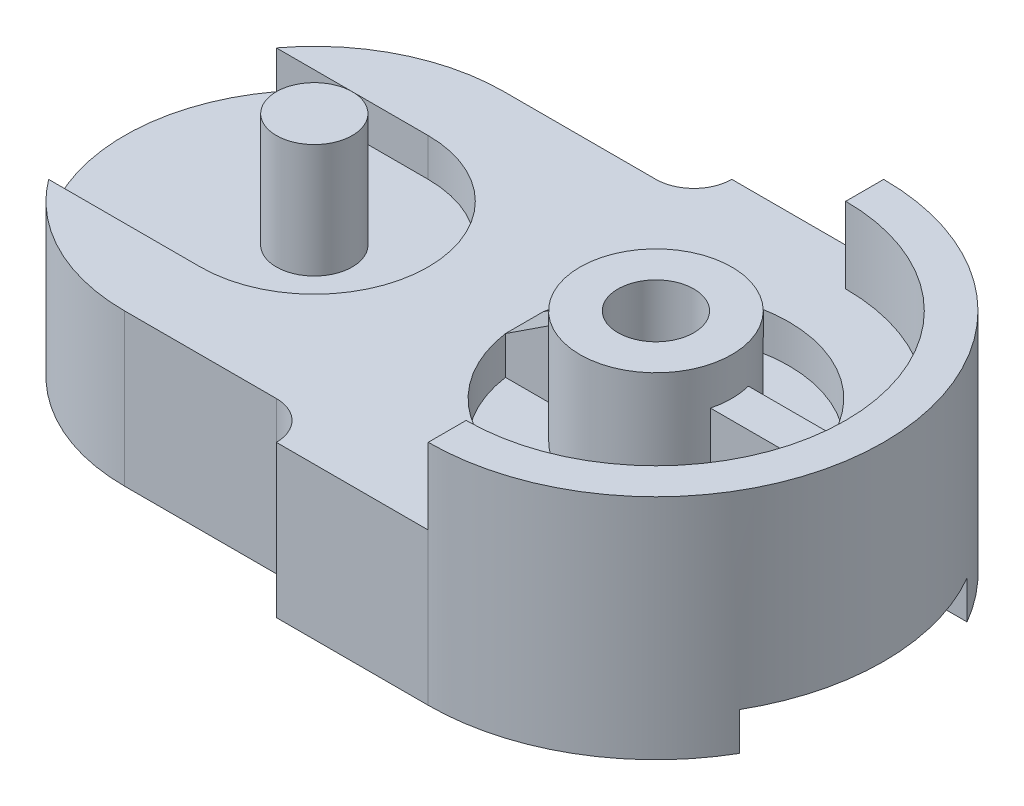
SolidWorks part; units mm, degrees
ref_plane "Front Plane" through (0, 0, 0) normal (0, 0, 1) x (1, 0, 0)
ref_plane "Top Plane" through (0, 0, 0) normal (0, 1, 0) x (1, 0, 0)
ref_plane "Right Plane" through (0, 0, 0) normal (1, 0, 0) x (0, 0, -1)
sketch "Sketch1" plane through (0, 0, 0) normal (0, 1, 0) x (1, 0, 0)
  line L1 (0, 0) -> (200, 0)
  line L2 (0, 0) -> (0, 120)
  line L3 (0, 120) -> (200, 120)
  line L4 (200, 0) -> (200, 120)
  dimension "D1" = 200
  dimension "D2" = 120
extrude "Boss-Extrude1" add sketch "Sketch1" along normal blind 40
sketch "Sketch2" plane through (0, 40, 0) normal (0, 1, 0) x (1, 0, 0)
  line L1 (0, 120) -> (0, 0) construction
  line L2 (50, 110) -> (0, 110)
  line L3 (0, 110) -> (0, 0)
  line L4 (0, 0) -> (90, 0)
  line L5 (0, 0) -> (200, 0) construction
  line L6 (0, 110) -> (0, 120)
  line L7 (0, 120) -> (90, 120)
  line L8 (200, 120) -> (0, 120) construction
  line L9 (50, 110) -> (90, 110)
  line L10 (90, 110) -> (90, 120)
  line L11 (50, 10) -> (90, 10)
  line L12 (90, 10) -> (90, 0)
  arc A0 (50, 110) -> (50, 10) centre (50, 60) ccw
  line M1 (0, 120) -> (0, 0)
  line M2 (0, 0) -> (200, 0)
  line M4 (200, 120) -> (0, 120)
  dimension "D2" = 50
  dimension "D1" = 50
  dimension "D3" = 50
  dimension "D4" = 60
  dimension "D5" = 60
  dimension "D6" = 90
  dimension "D7" = 90
  dimension "D8" = 10
  dimension "D9" = 10
extrude "Cut-Extrude2" cut sketch "Sketch2" against normal blind 40 contours L9 L10 L2 M4 M1 | A0 L2 M1 | A0 L3 L12 L11 M2
sketch "Sketch3" plane through (0, 40, 0) normal (0, 1, 0) x (1, 0, 0)
  line L0 (90, 110) -> (90, 120)
  line L1 (90, 120) -> (100, 120)
  arc A0 (90, 110) -> (100, 120) centre (90, 120) ccw
  dimension "D1" = 10
  dimension "D2" = 10
extrude "Cut-Extrude3" cut sketch "Sketch3" against normal blind 40
sketch "Sketch4" plane through (0, 40, 0) normal (0, 1, 0) x (1, 0, 0)
  line L0 (90, 0) -> (200, 0) construction
  line L1 (90, 10) -> (90, 0)
  line L2 (90, 0) -> (100, 0)
  arc A0 (90, 10) -> (100, 0) centre (90, 0) cw
extrude "Cut-Extrude4" cut sketch "Sketch4" against normal blind 40
sketch "Sketch5" plane through (0, 0, 0) normal (0, -1, 0) x (1, 0, 0)
  line L0 (200, 0) -> (200, -120) construction
  line L1 (200, -30) -> (-8.73, -30)
  line L2 (200, -30) -> (200, -90)
  line L3 (200, -90) -> (-8.73, -90)
  line L4 (-8.73, -30) -> (-8.73, -90)
  line L5 (50, -110) -> (90, -110) construction
  arc A0 (50, -10) -> (50, -110) centre (50, -60) ccw construction
  dimension "D1" = 60
  dimension "D2" = 20
  dimension "D3" = 58.73
extrude "Cut-Extrude5" cut sketch "Sketch5" against normal blind 10
sketch "Sketch6" plane through (0, 40, 0) normal (0, 1, 0) x (1, 0, 0)
  line L0 (200, 120) -> (100, 120) construction
  line L1 (100, 0) -> (200, 0) construction
  line L2 (140, 120) -> (200, 120)
  line L3 (200, 120) -> (200, 0)
  line L4 (200, 0) -> (140, 0)
  arc A0 (140, 120) -> (140, 0) centre (140, 60) cw
  line M3 (100, 0) -> (200, 0)
  line M4 (200, 0) -> (200, 120)
  line M5 (200, 120) -> (100, 120)
  dimension "D3" = 60
  dimension "D1" = 40
  dimension "D2" = 40
  dimension "D4" = 60
extrude "Cut-Extrude6" cut sketch "Sketch6" against normal blind 116 contours A0 L3 M5 | A0 M4 M3
sketch "Sketch7" plane through (0, 40, 0) normal (0, 1, 0) x (1, 0, 0)
  line L0 (140, 110) -> (140, 120)
  line L1 (140, 10) -> (140, 0)
  arc A0 (140, 120) -> (140, 0) centre (140, 60) cw
  arc A1 (140, 0) -> (140, 120) centre (140, 60) ccw construction
  arc A2 (140, 110) -> (140, 10) centre (140, 60) cw
  dimension "D1" = 10
  dimension "D2" = 10
extrude "Boss-Extrude2" add sketch "Sketch7" along normal blind 20
sketch "Sketch8" plane through (0, 40, 0) normal (0, 1, 0) x (1, 0, 0)
  line L0 (10, 90) -> (50, 90)
  line L1 (10, 30) -> (50, 30)
  line L2 (50, 90) -> (10, 90)
  arc A0 (50, 110) -> (50, 10) centre (50, 60) ccw
  arc A1 (50, 110) -> (50, 10) centre (50, 60) ccw construction
  arc A2 (50, 90) -> (50, 30) centre (50, 60) cw
  point P14 (80, 60)
  arc M9 (50, 110) -> (50, 10) centre (50, 60) ccw
  dimension "D1" = 20
  dimension "D2" = 20
  dimension "D3" = 40
  dimension "D4" = 40
  dimension "D5" = 0
extrude "Cut-Extrude7" cut sketch "Sketch8" against normal blind 10 contours A2 L0 L1 M9
sketch "Sketch9" plane through (0, 30, 0) normal (0, 1, 0) x (1, 0, 0)
  circle A0 centre (50, 60) radius 10
  dimension "D1" = 20
extrude "Boss-Extrude3" add sketch "Sketch9" along normal blind 30
sketch "Sketch10" plane through (0, 40, 0) normal (0, 1, 0) x (1, 0, 0)
  line L0 (100, 0) -> (140, 0) construction
  circle A0 centre (140, 60) radius 10
  dimension "D1" = 20
  dimension "D2" = 60
  dimension "D3" = 0
extrude "Cut-Extrude8" cut sketch "Sketch10" against normal blind 69
sketch "Sketch11" plane through (0, 40, 0) normal (0, 1, 0) x (1, 0, 0)
  circle A0 centre (140, 60) radius 10
  circle A1 centre (140, 60) radius 20
  dimension "D1" = 20
  dimension "D2" = 40
extrude "Boss-Extrude4" add sketch "Sketch11" along normal blind 20
sketch "Sketch12" plane through (0, 40, 0) normal (0, 1, 0) x (1, 0, 0)
  circle A0 centre (140, 60) radius 20
  circle A1 centre (140, 60) radius 35
  dimension "D1" = 40
  dimension "D2" = 70
extrude "Cut-Extrude9" cut sketch "Sketch12" against normal blind 10
sketch "Sketch14" plane through (0, 40, 0) normal (0, 1, 0) x (1, 0, 0)
  line L0 (158.9485, 65) -> (160, 65)
  line L1 (189.7494, 65) -> (160, 65)
  line L3 (189.7494, 55) -> (160, 55)
  line L4 (160, 65) -> (160, 55)
  line L5 (158.9485, 55) -> (160, 55)
  arc A0 (140, 10) -> (140, 110) centre (140, 60) ccw construction
  circle A1 centre (140, 60) radius 20 construction
  arc A2 (158.9485, 65) -> (158.9485, 55) centre (140, 60) cw
  arc A3 (189.7494, 65) -> (189.7494, 55) centre (140, 60) cw
  circle M1 centre (140, 60) radius 35
  arc M9 (140, 10) -> (140, 110) centre (140, 60) ccw
  dimension "D3" = 19.5971
  dimension "D1" = 10
  dimension "D2" = 55
extrude "Boss-Extrude10" add sketch "Sketch14" along normal blind 10 and the other way blind 36 contours L1 L4 L3 M1 | L0 A2 L5 L4 | L3 L1 M9 M1
sketch "Sketch15" plane through (0, 30, 0) normal (0, 1, 0) x (1, 0, 0)
  line L1 (120.6351, 65) -> (105, 65)
  line L2 (120.6351, 65) -> (120.6351, 55)
  line L3 (120.6351, 55) -> (105, 55)
  arc A0 (159.3649, 65) -> (159.3649, 55) centre (140, 60) ccw construction
  arc A2 (120.6351, 65) -> (120.6351, 55) centre (140, 60) ccw
  arc A3 (105, 65) -> (105, 55) centre (140, 60) ccw
  arc M2 (174.641, 65) -> (174.641, 55) centre (140, 60) ccw
  arc M4 (159.3649, 55) -> (159.3649, 65) centre (140, 60) cw
  dimension "D3" = 35.3553
  dimension "D1" = 10
  dimension "D2" = 55
extrude "Boss-Extrude11" add sketch "Sketch15" along normal blind 20 contours L2 M4 | L3 L1 M4 M2
sketch "Sketch16" plane through (0, 0, -55) normal (0, 0, 1) x (1, 0, 0)
  line L0 (120.6351, 50) -> (105.359, 40)
  line L1 (105.359, 40) -> (105.359, 50)
  line L2 (105.359, 50) -> (120.6351, 50)
extrude "Cut-Extrude10" cut sketch "Sketch16" against normal blind 20
sketch "Sketch17" plane through (105.359, 0, 0) normal (1, 0, 0) x (0, 0, -1)
  line L1 (65, 50) -> (55, 50)
  line L2 (65, 50) -> (65, 40)
  line L3 (65, 40) -> (55, 40)
  line L4 (55, 50) -> (55, 40)
extrude "Cut-Extrude11" cut sketch "Sketch17" against normal blind 20
sketch "Sketch18" plane through (0, 10, 0) normal (0, -1, 0) x (1, 0, 0)
  line L1 (191.9615, -30) -> (10, -30)
  line L2 (191.9615, -30) -> (191.9615, -90)
  line L3 (191.9615, -90) -> (10, -90)
  line L4 (10, -30) -> (10, -90)
extrude "Cut-Extrude12" cut sketch "Sketch18" along normal blind 20
